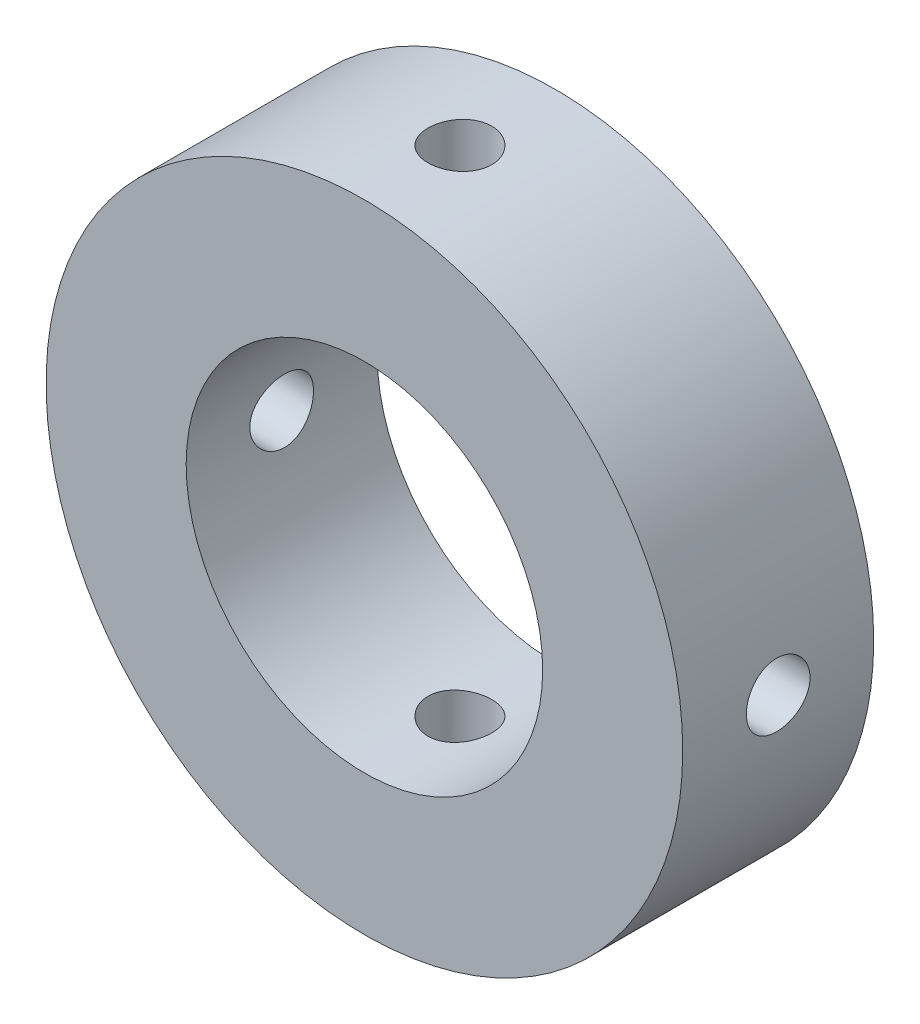
SolidWorks part; units mm, degrees
ref_plane "前视基准面" through (0, 0, 0) normal (0, 0, 1) x (1, 0, 0)
ref_plane "上视基准面" through (0, 0, 0) normal (0, 1, 0) x (1, 0, 0)
ref_plane "右视基准面" through (0, 0, 0) normal (1, 0, 0) x (0, 0, -1)
sketch "草图1" plane through (0, 0, 0) normal (0, 0, 1) x (1, 0, 0)
  circle A0 centre (0, 0) radius 2.8
  circle A1 centre (0, 0) radius 5
extrude "凸台-拉伸1" add sketch "草图1" along normal blind 3
sketch "草图2" plane through (0, 0, 0) normal (0, 1, 0) x (1, 0, 0)
  circle A0 centre (0, -1.5) radius 0.5
extrude "切除-拉伸1" cut sketch "草图2" against normal mid plane 13
sketch "草图3" plane through (0, 0, 0) normal (1, 0, 0) x (0, 0, -1)
  circle A0 centre (-1.5, 0) radius 0.5
extrude "切除-拉伸2" cut sketch "草图3" against normal mid plane 13
